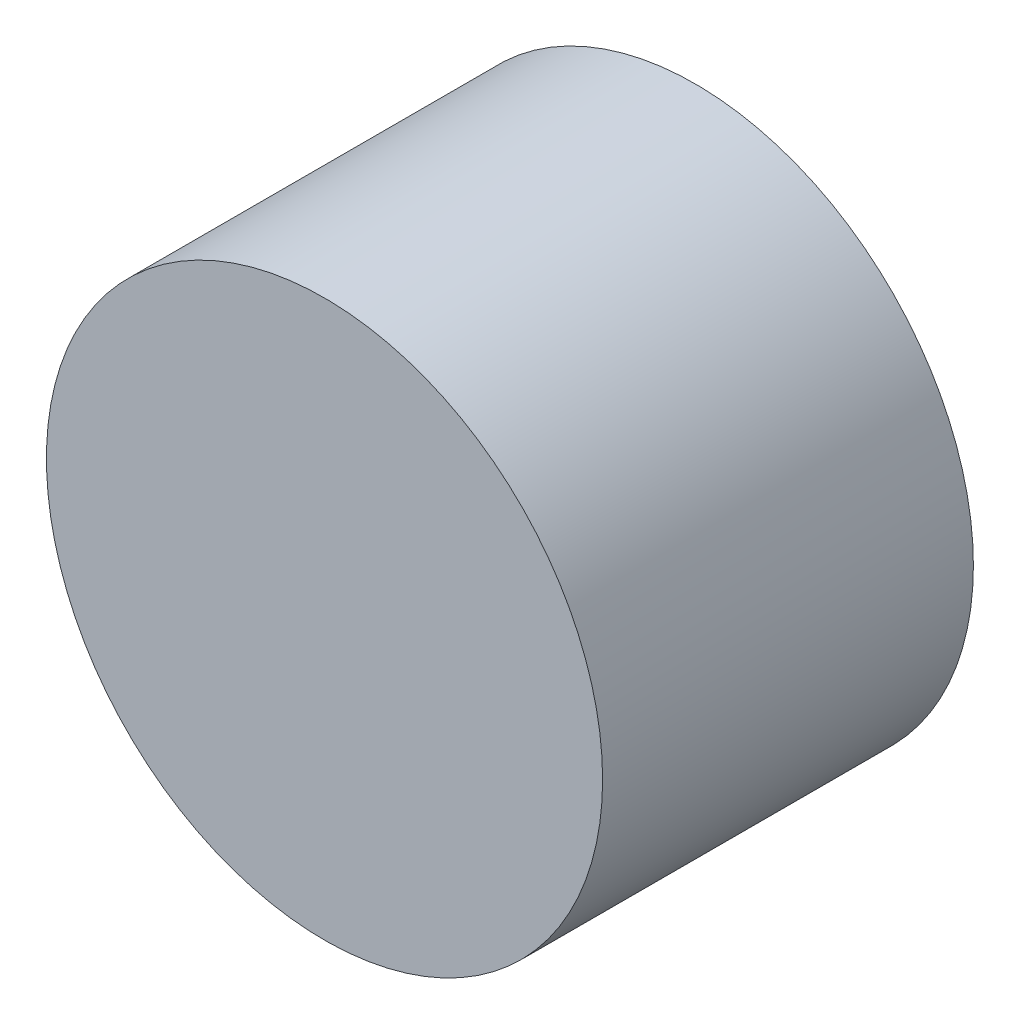
SolidWorks part; units mm, degrees
material "Nylon 101"
ref_plane "Front Plane" through (0, 0, 0) normal (0, 0, 1) x (1, 0, 0)
ref_plane "Top Plane" through (0, 0, 0) normal (0, 1, 0) x (1, 0, 0)
ref_plane "Right Plane" through (0, 0, 0) normal (1, 0, 0) x (0, 0, -1)
sketch "Sketch1" plane through (0, 0, 0) normal (0, 0, 1) x (1, 0, 0)
  circle A0 centre (0, 0) radius 7.5
  point P3 (0, 0)
  dimension "D1" = 15
extrude "Boss-Extrude1" add sketch "Sketch1" along normal blind 10
